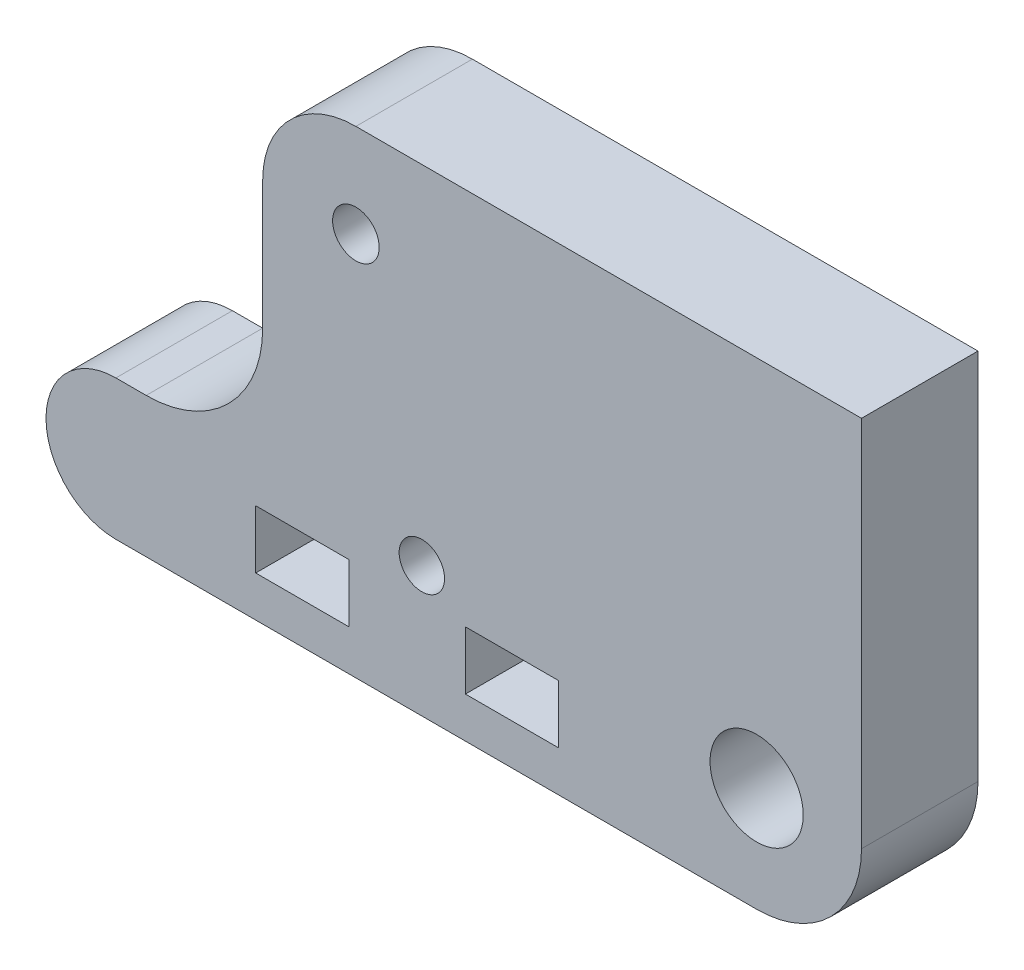
SolidWorks part; units mm, degrees
ref_plane "Płaszczyzna przednia" through (0, 0, 0) normal (0, 0, 1) x (1, 0, 0)
ref_plane "Płaszczyzna górna" through (0, 0, 0) normal (0, 1, 0) x (1, 0, 0)
ref_plane "Płaszczyzna prawa" through (0, 0, 0) normal (1, 0, 0) x (0, 0, -1)
sketch "Sketch 1" plane through (0, 0, 0) normal (0, 0, 1) x (1, 0, 0)
  line L0 (-27.5, 0) -> (27.5, 0)
  line L1 (-27.5, 12) -> (-24.9, 12)
  line L2 (-14.9, 22) -> (-14.9, 33)
  line L3 (1.1, 33) -> (1.1, 28)
  line L4 (11.1, 18) -> (27.5, 18)
  line L5 (-6.9, 41) -> (36.5, 41)
  line L6 (-15.5, 8.5) -> (-7.5, 8.5)
  line L7 (-15.5, 8.5) -> (-15.5, 3.5)
  line L8 (-15.5, 3.5) -> (-7.5, 3.5)
  line L9 (-7.5, 8.5) -> (-7.5, 3.5)
  line L10 (2.5, 8.5) -> (10.5, 8.5)
  line L11 (2.5, 8.5) -> (2.5, 3.5)
  line L12 (2.5, 3.5) -> (10.5, 3.5)
  line L13 (10.5, 8.5) -> (10.5, 3.5)
  line L14 (36.5, 41) -> (36.5, 9)
  arc A0 (27.5, 0) -> (27.5, 18) centre (27.5, 9) ccw
  arc A1 (-27.5, 0) -> (-27.5, 12) centre (-27.5, 6) cw
  circle A3 centre (27.5, 9) radius 4
  circle A4 centre (-6.9, 33) radius 2
  circle A5 centre (-6.9, 33) radius 8 construction
  arc A6 (-14.9, 33) -> (1.1, 33) centre (-6.9, 33) cw
  arc A7 (1.1, 28) -> (11.1, 18) centre (11.1, 28) ccw
  arc A8 (-24.9, 12) -> (-14.9, 22) centre (-24.9, 22) ccw
  circle A10 centre (-1.2382, 11.1833) radius 1.95 construction
  circle A12 centre (-1.2382, 11.1833) radius 1.95
  point P25 (-15.5, 6)
  dimension "D2" = 6
  dimension "D3" = 9
  dimension "D4" = 8
  dimension "D7" = 6.9
  dimension "D8" = 16
  dimension "D9" = 10
  dimension "D1" = 55
  dimension "D6" = 33
  dimension "D10" = 8
  dimension "D11" = 5
  dimension "D12" = 12
  dimension "D13" = 10
extrude "Boss-Extrude1" add sketch "Sketch 1" along normal blind 10
